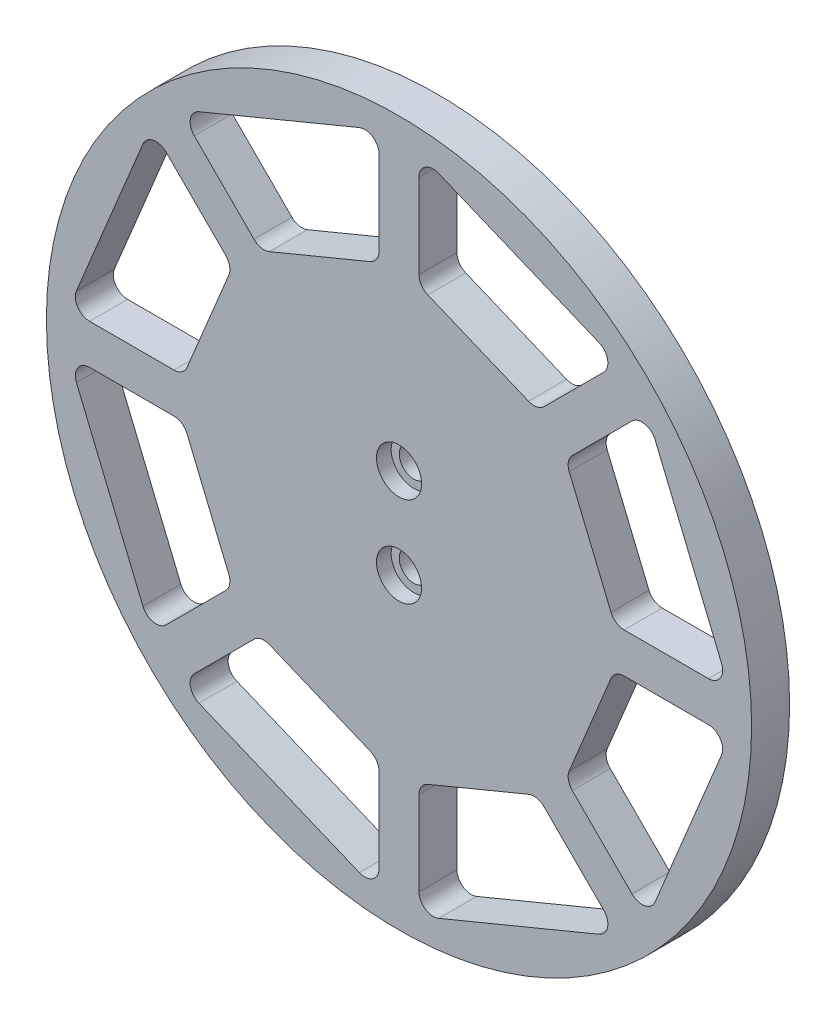
SolidWorks part; units mm, degrees
ref_plane "Front Plane" through (0, 0, 0) normal (0, 0, 1) x (1, 0, 0)
ref_plane "Top Plane" through (0, 0, 0) normal (0, 1, 0) x (1, 0, 0)
ref_plane "Right Plane" through (0, 0, 0) normal (1, 0, 0) x (0, 0, -1)
sketch "Sketch1" plane through (0, 0, 0) normal (0, 0, 1) x (1, 0, 0)
  line L0 (0, 9.5) -> (0, -9.5) construction
  line L7 (67.9259, 8.3481) -> (53.9338, 42.1279)
  line L8 (42.1279, 53.9338) -> (8.3481, 67.9259)
  line L9 (-8.3481, 67.9259) -> (-42.1279, 53.9338)
  line L10 (-53.9338, 42.1279) -> (-67.9259, 8.3481)
  line L11 (-67.9259, -8.3481) -> (-53.9338, -42.1279)
  line L12 (-42.1279, -53.9338) -> (-8.3481, -67.9259)
  line L13 (8.3481, -67.9259) -> (42.1279, -53.9338)
  line L14 (53.9338, -42.1279) -> (67.9259, -8.3481)
  line L15 (44.6314, 6.0519) -> (35.8385, 27.2798)
  line L16 (27.2798, 35.8385) -> (6.0519, 44.6314)
  line L17 (-6.0519, 44.6314) -> (-27.2798, 35.8385)
  line L18 (-35.8385, 27.2798) -> (-44.6314, 6.0519)
  line L19 (-44.6314, -6.0519) -> (-35.8385, -27.2798)
  line L20 (-27.2798, -35.8385) -> (-6.0519, -44.6314)
  line L21 (6.0519, -44.6314) -> (27.2798, -35.8385)
  line L22 (35.8385, -27.2798) -> (44.6314, -6.0519)
  line L48 (43.1012, -49.0409) -> (30.5491, -36.4888)
  line L51 (-30.5491, -36.4888) -> (-43.1012, -49.0409)
  line L53 (-47.403, -4.2) -> (-65.1543, -4.2)
  line L57 (-36.4888, 30.5491) -> (-49.0409, 43.1012)
  line L59 (-36.4888, -30.5491) -> (-49.0409, -43.1012)
  line L62 (-47.403, 4.2) -> (-65.1543, 4.2)
  line L63 (-30.5491, 36.4888) -> (-43.1012, 49.0409)
  line L65 (-4.2, -65.1543) -> (-4.2, -47.403)
  line L68 (4.2, -65.1543) -> (4.2, -47.403)
  line L73 (49.0409, -43.1012) -> (36.4888, -30.5491)
  line L75 (65.1543, -4.2) -> (47.403, -4.2)
  line L77 (65.1543, 4.2) -> (47.403, 4.2)
  line L79 (49.0409, 43.1012) -> (36.4888, 30.5491)
  line L81 (43.1012, 49.0409) -> (30.5491, 36.4888)
  line L83 (4.2, 65.1543) -> (4.2, 47.403)
  line L85 (-4.2, 65.1543) -> (-4.2, 47.403)
  circle A0 centre (0, 0) radius 74.25
  arc A1 (-49.5089, 43.5692) -> (-65.8161, 4.2) centre (0, 0) ccw construction
  arc A2 (-49.5089, 43.5692) -> (-65.8161, 4.2) centre (0, 0) ccw construction
  arc A3 (-33.6208, 27.6811) -> (-43.347, 4.2) centre (0, 0) ccw construction
  circle A4 centre (0, 0) radius 65.95 construction
  arc A5 (-43.347, -4.2) -> (-33.6208, -27.6811) centre (0, 0) ccw construction
  arc A6 (-65.8161, -4.2) -> (-4.2, -65.8161) centre (0, 0) ccw construction
  arc A7 (-65.8161, -4.2) -> (-4.2, -65.8161) centre (0, 0) ccw construction
  arc A8 (-67.9259, -8.3481) -> (-65.1543, -4.2) centre (-65.1543, -7.2) cw
  arc A9 (-4.2, 65.8161) -> (-43.5692, 49.5089) centre (0, 0) ccw construction
  arc A10 (-4.2, 65.8161) -> (-43.5692, 49.5089) centre (0, 0) ccw construction
  arc A11 (-44.6314, -6.0519) -> (-47.403, -4.2) centre (-47.403, -7.2) ccw
  arc A12 (43.347, 4.2) -> (40.235, 16.6659) centre (0, 0) ccw construction
  arc A13 (65.8161, 4.2) -> (4.2, 65.8161) centre (0, 0) ccw construction
  arc A14 (65.8161, 4.2) -> (4.2, 65.8161) centre (0, 0) ccw construction
  arc A15 (4.2, -65.8161) -> (65.8161, -4.2) centre (0, 0) ccw construction
  arc A16 (4.2, -65.8161) -> (65.8161, -4.2) centre (0, 0) ccw construction
  arc A17 (-27.6811, -33.6208) -> (43.347, -4.2) centre (0, 0) ccw construction
  arc A18 (-35.8385, -27.2798) -> (-36.4888, -30.5491) centre (-38.6102, -28.4278) cw
  arc A19 (-53.9338, -42.1279) -> (-49.0409, -43.1012) centre (-51.1622, -40.9798) ccw
  arc A20 (-42.1279, -53.9338) -> (-43.1012, -49.0409) centre (-40.9798, -51.1622) cw
  arc A21 (-27.2798, -35.8385) -> (-30.5491, -36.4888) centre (-28.4278, -38.6102) ccw
  arc A22 (-6.0519, -44.6314) -> (-4.2, -47.403) centre (-7.2, -47.403) cw
  arc A23 (-8.3481, -67.9259) -> (-4.2, -65.1543) centre (-7.2, -65.1543) ccw
  arc A24 (8.3481, -67.9259) -> (4.2, -65.1543) centre (7.2, -65.1543) cw
  arc A25 (6.0519, -44.6314) -> (4.2, -47.403) centre (7.2, -47.403) ccw
  arc A26 (27.2798, -35.8385) -> (30.5491, -36.4888) centre (28.4278, -38.6102) cw
  arc A27 (42.1279, -53.9338) -> (43.1012, -49.0409) centre (40.9798, -51.1622) ccw
  arc A28 (35.8385, -27.2798) -> (36.4888, -30.5491) centre (38.6102, -28.4278) ccw
  arc A29 (44.6314, -6.0519) -> (47.403, -4.2) centre (47.403, -7.2) cw
  arc A30 (53.9338, -42.1279) -> (49.0409, -43.1012) centre (51.1622, -40.9798) cw
  arc A31 (67.9259, -8.3481) -> (65.1543, -4.2) centre (65.1543, -7.2) ccw
  arc A32 (53.9338, 42.1279) -> (49.0409, 43.1012) centre (51.1622, 40.9798) ccw
  arc A33 (67.9259, 8.3481) -> (65.1543, 4.2) centre (65.1543, 7.2) cw
  arc A34 (44.6314, 6.0519) -> (47.403, 4.2) centre (47.403, 7.2) ccw
  arc A35 (35.8385, 27.2798) -> (36.4888, 30.5491) centre (38.6102, 28.4278) cw
  arc A36 (27.2798, 35.8385) -> (30.5491, 36.4888) centre (28.4278, 38.6102) ccw
  arc A37 (42.1279, 53.9338) -> (43.1012, 49.0409) centre (40.9798, 51.1622) cw
  arc A38 (8.3481, 67.9259) -> (4.2, 65.1543) centre (7.2, 65.1543) ccw
  arc A39 (6.0519, 44.6314) -> (4.2, 47.403) centre (7.2, 47.403) cw
  arc A40 (-6.0519, 44.6314) -> (-4.2, 47.403) centre (-7.2, 47.403) ccw
  arc A41 (-8.3481, 67.9259) -> (-4.2, 65.1543) centre (-7.2, 65.1543) cw
  arc A42 (-42.1279, 53.9338) -> (-43.1012, 49.0409) centre (-40.9798, 51.1622) ccw
  arc A43 (-27.2798, 35.8385) -> (-30.5491, 36.4888) centre (-28.4278, 38.6102) cw
  arc A44 (-35.8385, 27.2798) -> (-36.4888, 30.5491) centre (-38.6102, 28.4278) ccw
  arc A45 (-53.9338, 42.1279) -> (-49.0409, 43.1012) centre (-51.1622, 40.9798) cw
  arc A46 (-67.9259, 8.3481) -> (-65.1543, 4.2) centre (-65.1543, 7.2) ccw
  arc A47 (-44.6314, 6.0519) -> (-47.403, 4.2) centre (-47.403, 7.2) cw
  circle A48 centre (0, 9.5) radius 3.05
  circle A49 centre (0, -9.5) radius 3.05
  point P60 (0, 0)
  point P104 (0, 0)
  dimension "D1" = 148.5
  dimension "D4" = 3
  dimension "D6" = 6.1
  dimension "D3" = 87.1
  dimension "D5" = 19
  dimension "D2" = 8.3
extrude "Boss-Extrude1" add sketch "Sketch1" along normal blind 8
sketch "Sketch2" plane through (0, 0, 8) normal (0, 0, 1) x (1, 0, 0)
  circle A0 centre (0, 9.5) radius 4.75
  circle A1 centre (0, -9.5) radius 4.75
  dimension "D1" = 9.5
extrude "Cut-Extrude1" cut sketch "Sketch2" against normal blind 3.1 contours A1 | A0
